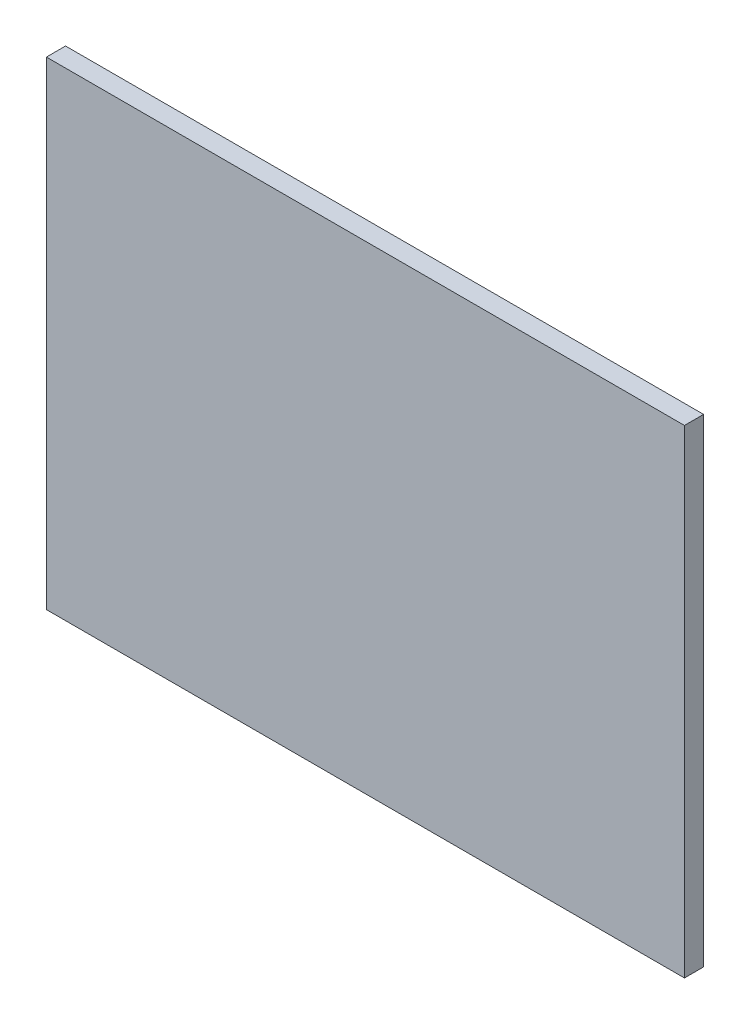
SolidWorks part; units mm, degrees
ref_plane "Front Plane" through (0, 0, 0) normal (0, 0, 1) x (1, 0, 0)
ref_plane "Top Plane" through (0, 0, 0) normal (0, 1, 0) x (1, 0, 0)
ref_plane "Right Plane" through (0, 0, 0) normal (1, 0, 0) x (0, 0, -1)
sketch "Croquis1" plane through (0, 0, 0) normal (0, 0, 1) x (1, 0, 0)
  line L1 (-50, 37.5) -> (50, 37.5)
  line L2 (-50, 37.5) -> (-50, -37.5)
  line L3 (-50, -37.5) -> (50, -37.5)
  line L4 (50, 37.5) -> (50, -37.5)
  point P0 (0, 0)
  dimension "D1" = 100
  dimension "D2" = 75
  dimension "D3" = 37.5
  dimension "D4" = 50
extrude "Saliente-Extruir1" add sketch "Croquis1" along normal blind 3
